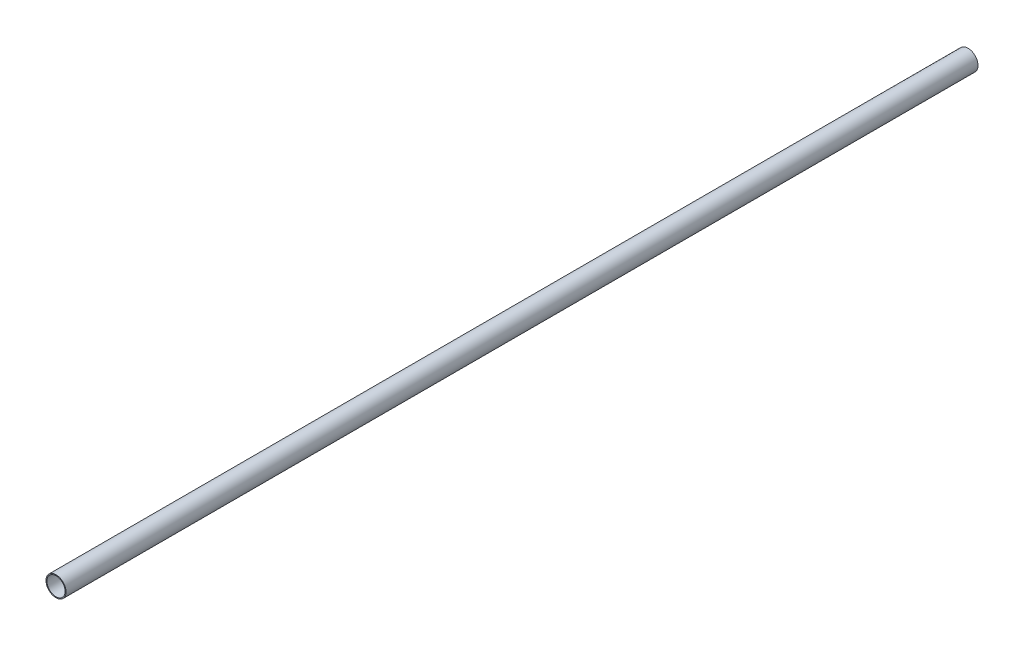
SolidWorks part; units mm, degrees
material "Carbon Fiber Tube - UD Approx"
ref_plane "Front Plane" through (0, 0, 0) normal (0, 0, 1) x (1, 0, 0)
ref_plane "Top Plane" through (0, 0, 0) normal (0, 1, 0) x (1, 0, 0)
ref_plane "Right Plane" through (0, 0, 0) normal (1, 0, 0) x (0, 0, -1)
sketch "Sketch1" plane through (0, 0, 0) normal (0, 0, 1) x (1, 0, 0)
  circle A0 centre (0, 0) radius 11
  circle A1 centre (0, 0) radius 10
  dimension "D1" = 22
  dimension "D2" = 20
extrude "Boss-Extrude1" add sketch "Sketch1" along normal blind 1000
